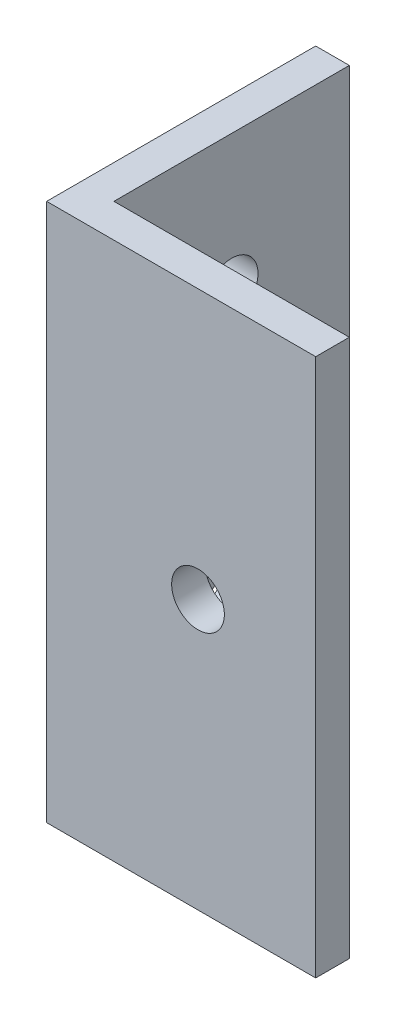
SolidWorks part; units mm, degrees
ref_plane "Front" through (0, 0, 0) normal (0, 0, 1) x (1, 0, 0)
ref_plane "Top" through (0, 0, 0) normal (0, 1, 0) x (1, 0, 0)
ref_plane "Right" through (0, 0, 0) normal (1, 0, 0) x (0, 0, -1)
sketch "Sketch1" plane through (0, 0, 0) normal (0, 1, 0) x (1, 0, 0)
  line L0 (3.175, 3.175) -> (25.4, 3.175)
  line L1 (0, 0) -> (25.4, 0)
  line L2 (0, 0) -> (0, 25.4)
  line L3 (0, 25.4) -> (25.4, 25.4) construction
  line L4 (25.4, 0) -> (25.4, 25.4) construction
  line L5 (3.175, 3.175) -> (3.175, 25.4)
  line L6 (0, 25.4) -> (3.175, 25.4)
  line L7 (25.4, 0) -> (25.4, 3.175)
  dimension "D1" = 25.4
  dimension "D2" = 25.4
  dimension "D3" = 3.175
extrude "Boss-Extrude1" add sketch "Sketch1" along normal blind 50.8
sketch "Sketch3" plane through (0, 0, -3.175) normal (0, 0, -1) x (-1, 0, 0)
  line L0 (-14.2875, 50.8) -> (-14.2875, 0) construction
  line L1 (-25.4, 50.8) -> (-3.175, 50.8) construction
  line L2 (-25.4, 0) -> (-3.175, 0) construction
  circle A0 centre (-14.2875, 25.4) radius 2.4892
  dimension "D1" = 4.9784
extrude "Cut-Extrude1" cut sketch "Sketch3" against normal through all
sketch "Sketch4" plane through (3.175, 0, 0) normal (1, 0, 0) x (0, 0, -1)
  line L0 (14.2875, 50.8) -> (14.2875, 0) construction
  line L1 (3.175, 50.8) -> (25.4, 50.8) construction
  line L2 (3.175, 0) -> (25.4, 0) construction
  circle A0 centre (14.2875, 12.7) radius 2.4892
  circle A1 centre (14.2875, 38.1) radius 2.4892
  dimension "D1" = 25.4
  dimension "D3" = 4.9784
  dimension "D2" = 12.7
extrude "Cut-Extrude2" cut sketch "Sketch4" against normal through all
sketch "Sketch5" [suppressed] plane through (0, 0, -3.175) normal (0, 0, -1) x (-1, 0, 0)
  line L0 (-12.7, 50.8) -> (-12.7, 0) construction
  line L1 (-25.4, 50.8) -> (-3.175, 50.8) construction
  line L4 (-25.4, 50.8) -> (-25.4, 0) construction
  circle A0 centre (-12.7, 12.7) radius 2.4892
  circle A1 centre (-12.7, 38.1) radius 2.4892
  dimension "D1" = 12.7
  dimension "D3" = 4.9784
  dimension "D2" = 25.4
  dimension "D4" = 12.7
extrude "Cut-Extrude3" [suppressed] cut sketch "Sketch5" against normal through all
sketch "Sketch6" [suppressed] plane through (3.175, 0, 0) normal (1, 0, 0) x (0, 0, -1)
  line L0 (14.2875, 50.8) -> (14.2875, 0) construction
  line L1 (3.175, 50.8) -> (25.4, 50.8) construction
  line L2 (3.175, 0) -> (25.4, 0) construction
  circle A0 centre (14.2875, 25.4) radius 2.4892
  dimension "D1" = 4.9784
extrude "Cut-Extrude4" [suppressed] cut sketch "Sketch6" against normal through all
